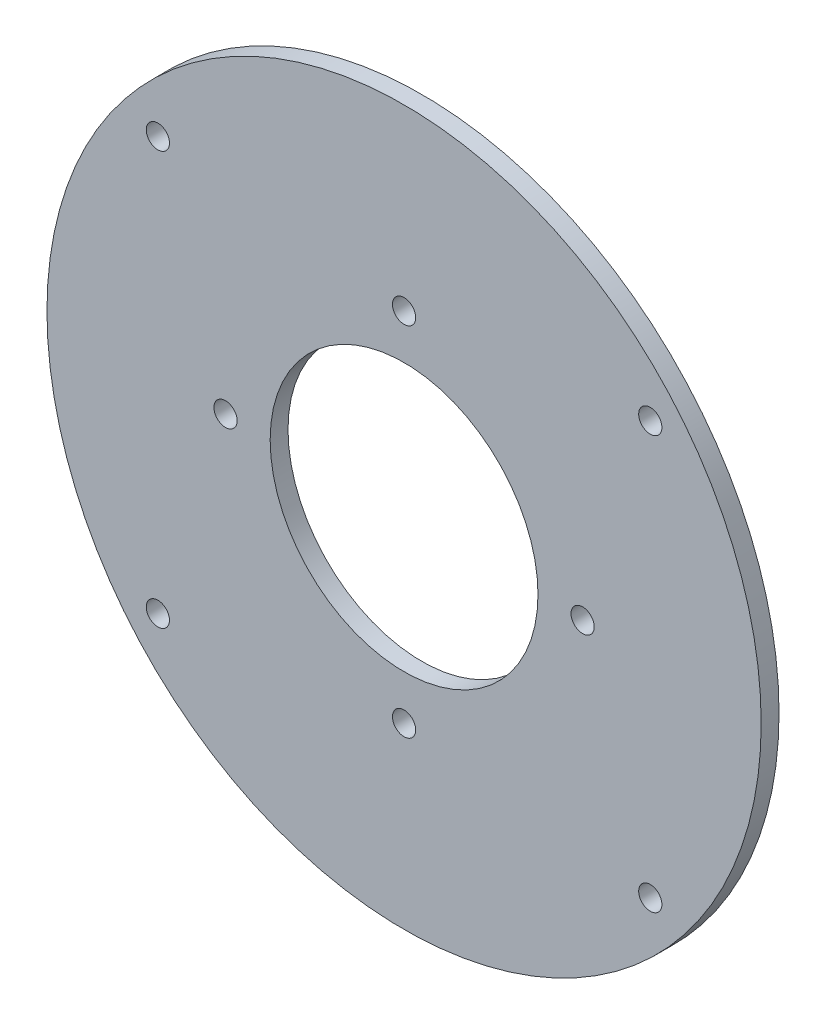
SolidWorks part; units mm, degrees
ref_plane "Front Plane" through (0, 0, 0) normal (0, 0, 1) x (1, 0, 0)
ref_plane "Top Plane" through (0, 0, 0) normal (0, 1, 0) x (1, 0, 0)
ref_plane "Right Plane" through (0, 0, 0) normal (1, 0, 0) x (0, 0, -1)
sketch "Sketch1" plane through (0, 0, 0) normal (0, 0, 1) x (1, 0, 0)
  line L0 (55.1552, -46.2807) -> (-55.1552, 46.2807) construction
  line L1 (-55.1552, -46.2807) -> (55.1552, 46.2807) construction
  line L2 (0, 0) -> (0, -40) construction
  line L3 (0, 0) -> (-40, 0) construction
  line L4 (0, 0) -> (0, 40) construction
  line L5 (0, 0) -> (40, 0) construction
  circle A0 centre (0, 0) radius 80
  circle A1 centre (-55.1552, 46.2807) radius 2.6
  circle A2 centre (55.1552, 46.2807) radius 2.6
  circle A3 centre (55.1552, -46.2807) radius 2.6
  circle A4 centre (-55.1552, -46.2807) radius 2.6
  circle A9 centre (0, 0) radius 30
  circle A10 centre (0, -40) radius 2.6
  circle A11 centre (-40, 0) radius 2.6
  circle A12 centre (0, 40) radius 2.6
  circle A13 centre (40, 0) radius 2.6
  point P6 (0, 0)
  point P9 (0, 0)
  dimension "D1" = 160
  dimension "D3" = 72
  dimension "D5" = 5.2
  dimension "D7" = 4
  dimension "D9" = 60
  dimension "D6" = 5.2
  dimension "D2" = 100
  dimension "D4" = 72
  dimension "D8" = 40
extrude "Boss-Extrude1" add sketch "Sketch1" along normal blind 4
